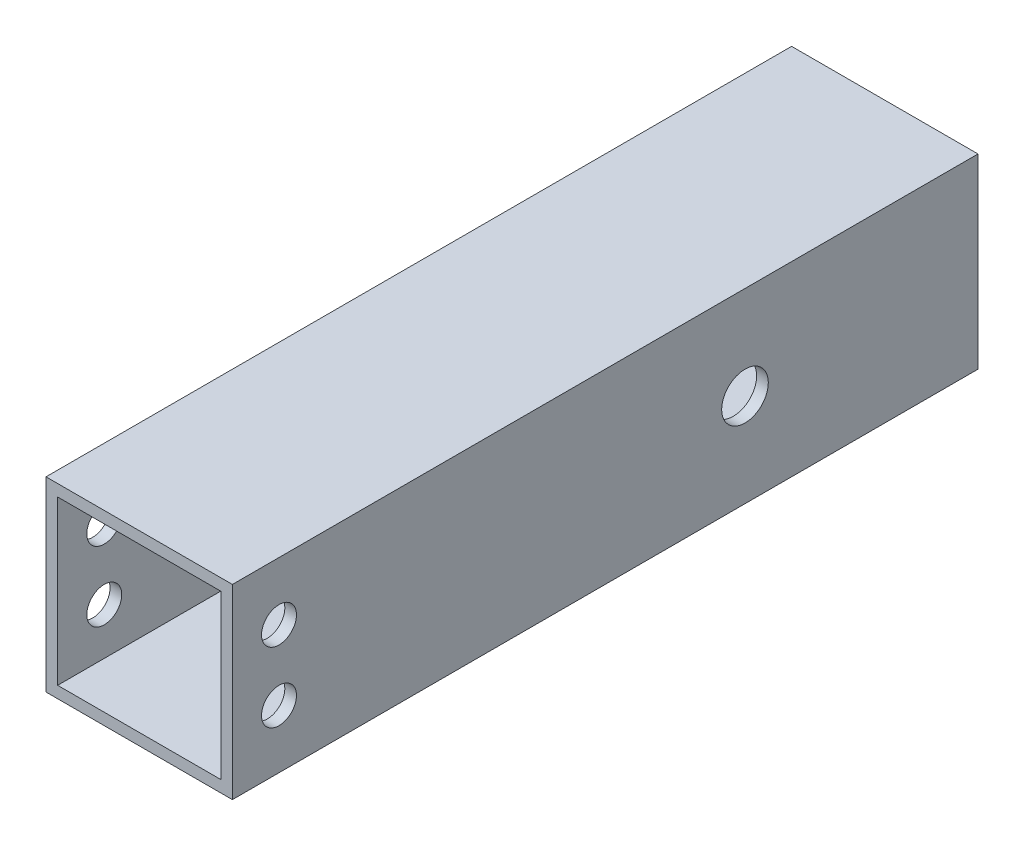
SolidWorks part; units mm, degrees
material "6061-T6 (SS)"
ref_plane "Front Plane" through (0, 0, 0) normal (0, 0, 1) x (1, 0, 0)
ref_plane "Top Plane" through (0, 0, 0) normal (0, 1, 0) x (1, 0, 0)
ref_plane "Right Plane" through (0, 0, 0) normal (1, 0, 0) x (0, 0, -1)
sketch "Sketch1" plane through (0, 0, 0) normal (0, 0, 1) x (1, 0, 0)
  line L1 (-11.1125, -11.1125) -> (11.1125, -11.1125)
  line L2 (-11.1125, -11.1125) -> (-11.1125, 11.1125)
  line L3 (-11.1125, 11.1125) -> (11.1125, 11.1125)
  line L4 (11.1125, -11.1125) -> (11.1125, 11.1125)
  line L5 (-11.1125, -11.1125) -> (11.1125, 11.1125) construction
  line L6 (-11.1125, 11.1125) -> (11.1125, -11.1125) construction
  line L7 (-12.7, -12.7) -> (12.7, -12.7)
  line L8 (-12.7, -12.7) -> (-12.7, 12.7)
  line L9 (-12.7, 12.7) -> (12.7, 12.7)
  line L10 (12.7, -12.7) -> (12.7, 12.7)
  line L11 (-12.7, -12.7) -> (12.7, 12.7) construction
  line L12 (-12.7, 12.7) -> (12.7, -12.7) construction
  point P0 (0, 0)
  point P6 (0, 0)
  dimension "D1" = 25.4
  dimension "D2" = 25.4
  dimension "D3" = 1.5875
  dimension "D4" = 1.5875
extrude "Boss-Extrude1" add sketch "Sketch1" along normal blind 101.6
sketch "Sketch2" plane through (12.7, 0, 0) normal (1, 0, 0) x (0, 0, -1)
  line L0 (-95.25, -4.7625) -> (-95.25, 4.7625) construction
  line L1 (0, -12.7) -> (0, 12.7) construction
  line L2 (-101.6, -12.7) -> (-101.6, 12.7) construction
  circle A0 centre (-95.25, 4.7625) radius 2.3813
  circle A1 centre (-95.25, -4.7625) radius 2.3813
  circle A2 centre (-31.75, 0) radius 3.175
  point P6 (-95.25, 0)
  point P8 (-9.8071, 0)
  dimension "D1" = 6.35
  dimension "D2" = 4.7625
  dimension "D3" = 4.7625
  dimension "D4" = 9.525
  dimension "D5" = 31.75
  dimension "D6" = 6.35
extrude "Cut-Extrude1" cut sketch "Sketch2" against normal up to surface (25.4 mm away) up to face at (-12.7, 0, 50.8)
